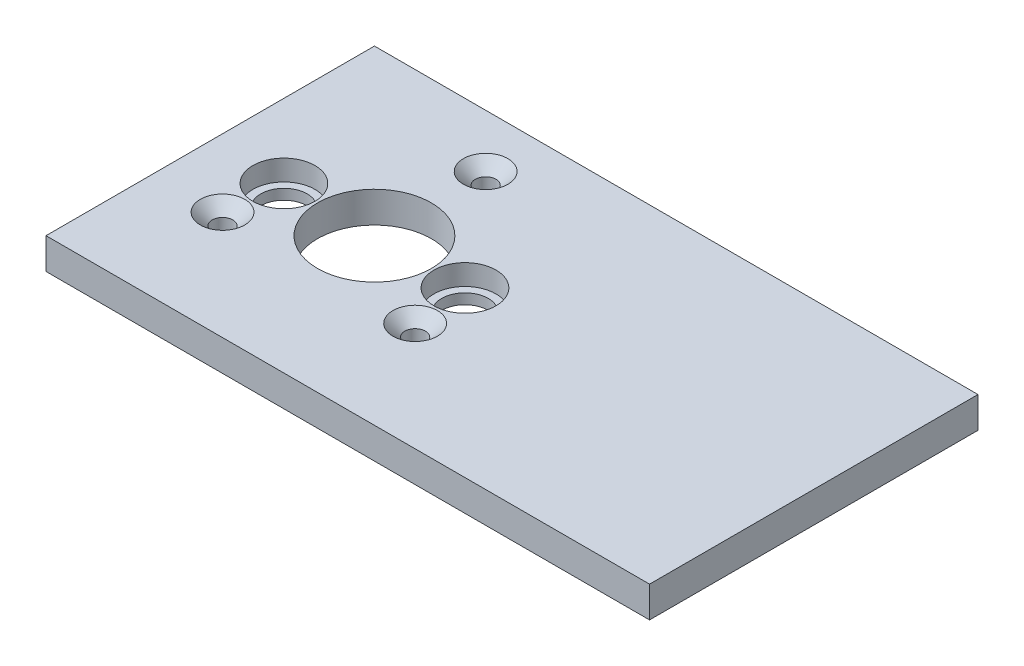
SolidWorks part; units mm, degrees
ref_plane "Front Plane" through (0, 0, 0) normal (0, 0, 1) x (1, 0, 0)
ref_plane "Top Plane" through (0, 0, 0) normal (0, 1, 0) x (1, 0, 0)
ref_plane "Right Plane" through (0, 0, 0) normal (1, 0, 0) x (0, 0, -1)
sketch "Sketch1" plane through (0, 0, 0) normal (0, 1, 0) x (1, 0, 0)
  line L1 (-31.75, 31.75) -> (84.9345, 31.75)
  line L2 (-31.75, 31.75) -> (-31.75, -31.75)
  line L3 (-31.75, -31.75) -> (84.9345, -31.75)
  line L4 (84.9345, 31.75) -> (84.9345, -31.75)
  circle A0 centre (0, 0) radius 11
  circle A1 centre (0, 0) radius 21.5 construction
  circle A2 centre (0, 0) radius 17.5 construction
  circle A3 centre (0, 21.5) radius 2
  circle A4 centre (18.6195, -10.75) radius 2
  circle A5 centre (-18.6195, -10.75) radius 2
  circle A6 centre (17.5, 0) radius 6
  circle A7 centre (-17.5, 0) radius 6
  dimension "D1" = 22
  dimension "D2" = 43
  dimension "D3" = 35
  dimension "D4" = 4
  dimension "D6" = 12
  dimension "D8" = 0
  dimension "D9" = 63.5
  dimension "D10" = 31.75
  dimension "D11" = 31.75
  dimension "D5" = 3
  dimension "D7" = 2
extrude "Boss-Extrude1" add sketch "Sketch1" along normal blind 6
chamfer "Chamfer1" distance 2.3 angle 45 3 edges at (18.6195, 6, 12.75) (0, 6, -19.5) (-18.6195, 6, 12.75)
sketch "Sketch2" plane through (0, 0, 0) normal (0, -1, 0) x (1, 0, 0)
  circle A0 centre (17.5, 0) radius 4.5
  circle A1 centre (-17.5, 0) radius 4.5
  circle A2 centre (-17.5, 0) radius 6
  circle A3 centre (17.5, 0) radius 6
  circle A4 centre (17.5, 0) radius 6 construction
  circle A5 centre (-17.5, 0) radius 6 construction
  dimension "D1" = 9
  dimension "D2" = 9
  dimension "D3" = 0
  dimension "D4" = 0
extrude "Boss-Extrude2" add sketch "Sketch2" against normal blind 2
